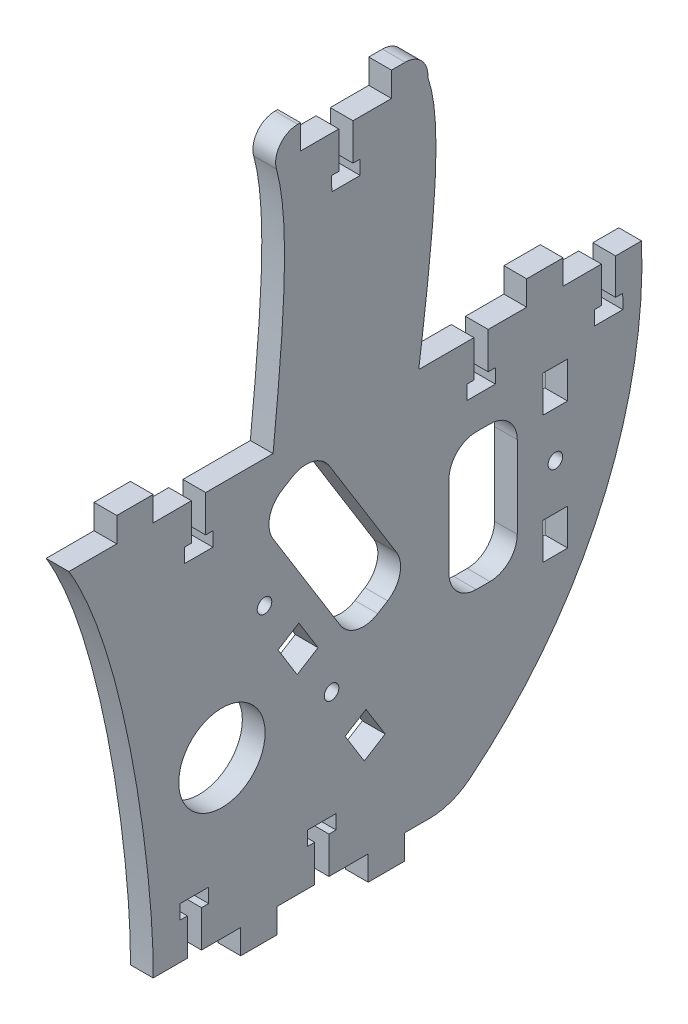
SolidWorks part; units mm, degrees
ref_plane "Front Plane" through (0, 0, 0) normal (0, 0, 1) x (1, 0, 0)
ref_plane "Top Plane" through (0, 0, 0) normal (0, 1, 0) x (1, 0, 0)
ref_plane "Right Plane" through (0, 0, 0) normal (1, 0, 0) x (0, 0, -1)
sketch "Sketch1" plane through (0, 0, 0) normal (1, 0, 0) x (0, 0, -1)
  line L0 (0, 110) -> (159.8137, 110)
  line L1 (106.68, 0) -> (0, 0)
  line L2 (0, 0) -> (0, 110)
  line L3 (36.2253, 95.776) -> (36.2253, 114.63) construction
  line L4 (74.3728, 96) -> (74.3728, 116.6546) construction
  line L5 (115.062, 95.776) -> (115.062, 119.2692) construction
  line L6 (23.5253, -5.9944) -> (23.5253, 146.3399) construction
  line L7 (35.0028, 14.224) -> (35.0028, 4.4881) construction
  line L8 (70.5628, 14.224) -> (70.5628, 4.0689) construction
  line L9 (77.3365, 179.3005) -> (77.3365, 182.7862) construction
  line L10 (61.2755, 63.6608) -> (66.6243, 55.0228) construction
  line L12 (85.3452, 24.7896) -> (40.7447, 96.8169) construction
  line L13 (56.9924, 110) -> (95.7389, 110)
  line L14 (135.7653, 91.7849) -> (135.7653, 46.0648) construction
  line L15 (0, 0) -> (4.645, 0)
  line L16 (0, 0) -> (0, 106.026)
  line L17 (64.6365, 179.3005) -> (90.0365, 179.3005)
  line L18 (77.3365, 165.0765) -> (77.3365, 176.5985) construction
  line L21 (150.622, 96) -> (150.622, 123.1211) construction
  line L22 (59.4414, 99.9132) -> (62.2149, 101.6307)
  line L23 (56.9744, 89.4231) -> (75.6953, 59.19)
  line L24 (86.1854, 56.723) -> (88.959, 58.4404)
  line L25 (72.705, 99.1637) -> (91.4259, 68.9306)
  line L27 (113.7019, 86.9157) -> (117.5119, 86.9157)
  line L28 (106.0819, 79.2957) -> (106.0819, 56.4357)
  line L29 (113.7019, 48.8157) -> (117.5119, 48.8157)
  line L30 (125.1319, 79.2957) -> (125.1319, 56.4357)
  arc A0 (159.8137, 110) -> (106.68, 0) centre (30.2941, 104.7297) cw
  circle A1 centre (73.3103, 44.2252) radius 2.032
  circle A2 centre (54.5895, 74.4584) radius 2.032
  arc A3 (72.705, 99.1637) -> (62.2149, 101.6307) centre (66.2265, 95.1521) ccw
  circle A4 centre (135.7653, 68.9249) radius 2.032
  arc A5 (56.9744, 89.4231) -> (59.4414, 99.9132) centre (63.453, 93.4347) cw
  arc A6 (86.1854, 56.723) -> (75.6953, 59.19) centre (82.1738, 63.2016) cw
  arc A7 (88.959, 58.4404) -> (91.4259, 68.9306) centre (84.9474, 64.919) ccw
  arc A8 (113.7019, 86.9157) -> (106.0819, 79.2957) centre (113.7019, 79.2957) ccw
  arc A9 (117.5119, 86.9157) -> (125.1319, 79.2957) centre (117.5119, 79.2957) cw
  arc A10 (125.1319, 56.4357) -> (117.5119, 48.8157) centre (117.5119, 56.4357) cw
  arc A11 (113.7019, 48.8157) -> (106.0819, 56.4357) centre (113.7019, 56.4357) cw
  circle A13 centre (42.7143, 43.634) radius 12.049
  spline S0 degree 3 poles (54.4765, 186.1585) (63.2335, 173.4813) (60.1129, 141.7407) (56.9924, 110) knots 0 0 0 0 1 1 1 1
  spline S1 degree 3 poles (23.5253, 0) (23.8864, 21.7728) (16.984, 81.5035) (0, 110) knots 0 0 0 0 1 1 1 1
  spline S2 degree 3 poles (94.1234, 188.6516) (104.3412, 179.5615) (104.713, 162.5405) (97.6324, 110) knots 0 0 0 0 1 1 1 1
  point P62 (95.4375, 62.4521)
  point P65 (106.0819, 86.9157)
  point P72 (106.0819, 48.8157)
  line B0 (34.2129, 110) -> (34.2129, 99.7448)
  line B1 (34.2129, 99.7448) -> (32.2286, 99.7448)
  line B2 (32.2286, 99.7448) -> (32.2566, 95.776)
  line B3 (32.2566, 95.776) -> (40.1941, 95.776)
  line B4 (40.1941, 95.776) -> (40.1661, 99.7448)
  line B5 (40.1661, 99.7448) -> (38.1817, 99.7448)
  line B6 (38.1817, 99.7448) -> (38.1817, 110)
  line B7 (18.4453, 116.858) -> (18.4453, 110) construction
  line B8 (13.3653, 116.858) -> (23.5253, 116.858)
  line B9 (13.3653, 116.858) -> (13.3653, 110)
  line B10 (13.3653, 110) -> (23.5253, 110)
  line B11 (23.5253, 116.858) -> (23.5253, 110)
  line B12 (113.0496, 110) -> (113.0496, 99.7448)
  line B13 (113.0496, 99.7448) -> (111.0652, 99.7448)
  line B14 (111.0652, 99.7448) -> (111.0932, 95.776)
  line B15 (111.0932, 95.776) -> (119.0307, 95.776)
  line B16 (119.0307, 95.776) -> (119.0027, 99.7448)
  line B17 (119.0027, 99.7448) -> (117.0183, 99.7448)
  line B18 (117.0183, 99.7448) -> (117.0183, 110)
  line B19 (1894.7464, 116.858) -> (1894.7464, 110) construction
  line B20 (1889.6664, 116.858) -> (1899.8264, 116.858)
  line B21 (1889.6664, 116.858) -> (1889.6664, 110)
  line B22 (1889.6664, 110) -> (1899.8264, 110)
  line B23 (1899.8264, 116.858) -> (1899.8264, 110)
  line B24 (132.3245, 86.7129) -> (139.1825, 86.697) construction
  line B25 (132.3127, 81.6329) -> (132.3363, 91.7929)
  line B26 (132.3127, 81.6329) -> (139.1707, 81.617)
  line B27 (139.1707, 81.617) -> (139.1943, 91.777)
  line B28 (132.3363, 91.7929) -> (139.1943, 91.777)
  line B29 (132.3245, 51.1368) -> (139.1825, 51.1527) construction
  line B30 (132.3363, 46.0568) -> (132.3127, 56.2168)
  line B31 (132.3363, 46.0568) -> (139.1943, 46.0728)
  line B32 (139.1943, 46.0728) -> (139.1707, 56.2327)
  line B33 (132.3127, 56.2168) -> (139.1707, 56.2327)
  line B34 (85.5861, 30.9138) -> (79.7554, 27.3034) construction
  line B35 (82.9117, 35.2329) -> (88.2605, 26.5948)
  line B36 (82.9117, 35.2329) -> (77.081, 31.6224)
  line B37 (77.081, 31.6224) -> (82.4298, 22.9844)
  line B38 (88.2605, 26.5948) -> (82.4298, 22.9844)
  line B39 (66.8652, 61.147) -> (61.0346, 57.5365) construction
  line B40 (64.1908, 65.466) -> (69.5397, 56.828)
  line B41 (64.1908, 65.466) -> (58.3602, 61.8556)
  line B42 (58.3602, 61.8556) -> (63.709, 53.2175)
  line B43 (69.5397, 56.828) -> (63.709, 53.2175)
  line B44 (132.842, 116.858) -> (132.842, 110) construction
  line B45 (127.762, 116.858) -> (137.922, 116.858)
  line B46 (127.762, 116.858) -> (127.762, 110)
  line B47 (127.762, 110) -> (137.922, 110)
  line B48 (137.922, 116.858) -> (137.922, 110)
  line B49 (168.402, 116.858) -> (168.402, 110) construction
  line B50 (163.322, 116.858) -> (173.482, 116.858)
  line B51 (163.322, 116.858) -> (163.322, 110)
  line B52 (163.322, 110) -> (173.482, 110)
  line B53 (173.482, 116.858) -> (173.482, 110)
  line B54 (148.6096, 110.224) -> (148.6096, 99.9687)
  line B55 (148.6096, 99.9687) -> (146.6252, 99.9687)
  line B56 (146.6252, 99.9687) -> (146.6532, 96)
  line B57 (146.6532, 96) -> (154.5907, 96)
  line B58 (154.5907, 96) -> (154.5627, 99.9687)
  line B59 (154.5627, 99.9687) -> (152.5783, 99.9687)
  line B60 (152.5783, 99.9687) -> (152.5783, 110.224)
  line B61 (59.5565, 186.1585) -> (59.5565, 179.3005) construction
  line B62 (54.4765, 186.1585) -> (64.6365, 186.1585)
  line B63 (54.4765, 186.1585) -> (54.4765, 179.3005)
  line B64 (54.4765, 179.3005) -> (64.6365, 179.3005)
  line B65 (64.6365, 186.1585) -> (64.6365, 179.3005)
  line B66 (95.1165, 186.1585) -> (95.1165, 179.3005) construction
  line B67 (90.0365, 186.1585) -> (100.1965, 186.1585)
  line B68 (90.0365, 186.1585) -> (90.0365, 179.3005)
  line B69 (90.0365, 179.3005) -> (100.1965, 179.3005)
  line B70 (100.1965, 186.1585) -> (100.1965, 179.3005)
  line B71 (37.0152, 0) -> (37.0152, 10.2552)
  line B72 (37.0152, 10.2552) -> (38.9996, 10.2552)
  line B73 (38.9996, 10.2552) -> (38.9716, 14.224)
  line B74 (38.9716, 14.224) -> (31.0341, 14.224)
  line B75 (31.0341, 14.224) -> (31.0621, 10.2553)
  line B76 (31.0621, 10.2553) -> (33.0465, 10.2553)
  line B77 (33.0465, 10.2553) -> (33.0465, 0)
  line B78 (72.5752, 0) -> (72.5752, 10.2552)
  line B79 (72.5752, 10.2552) -> (74.5596, 10.2552)
  line B80 (74.5596, 10.2552) -> (74.5316, 14.224)
  line B81 (74.5316, 14.224) -> (66.5941, 14.224)
  line B82 (66.5941, 14.224) -> (66.6221, 10.2552)
  line B83 (66.6221, 10.2552) -> (68.6065, 10.2552)
  line B84 (68.6065, 10.2552) -> (68.6065, 0)
  line B85 (88.5968, 0) -> (88.5968, -6.858) construction
  line B86 (83.5168, 0) -> (93.6768, 0)
  line B87 (83.5168, 0) -> (83.5168, -6.858)
  line B88 (83.5168, -6.858) -> (93.6768, -6.858)
  line B89 (93.6768, 0) -> (93.6768, -6.858)
  line B90 (53.0368, 0) -> (53.0368, -6.858) construction
  line B91 (47.9568, 0) -> (58.1168, 0)
  line B92 (47.9568, 0) -> (47.9568, -6.858)
  line B93 (47.9568, -6.858) -> (58.1168, -6.858)
  line B94 (58.1168, 0) -> (58.1168, -6.858)
  line B95 (75.324, 179.3005) -> (75.324, 169.0452)
  line B96 (75.324, 169.0452) -> (73.3397, 169.0452)
  line B97 (73.3397, 169.0452) -> (73.3677, 165.0765)
  line B98 (73.3677, 165.0765) -> (81.3052, 165.0765)
  line B99 (81.3052, 165.0765) -> (81.2772, 169.0452)
  line B100 (81.2772, 169.0452) -> (79.2928, 169.0452)
  line B101 (79.2928, 169.0452) -> (79.2928, 179.3005)
  dimension "D15" = 17.78
  dimension "D14" = 17.78
  dimension "D33" = 4.064
  dimension "D34" = 4.064
  dimension "D35" = 4.064
  dimension "D2" = 110
  dimension "D3" = 106.68
  dimension "D5" = 17.78
  dimension "D6" = 17.78
  dimension "D7" = 160.1167
  dimension "D8" = 17.78
  dimension "D9" = 17.78
  dimension "D10" = 76.2
  dimension "D11" = 17.78
  dimension "D12" = 17.78
  dimension "D13" = 17.78
  dimension "D26" = 25.4
  dimension "D31" = 40.64
sketch_block_instance "Block1-1"
sketch_block "Block1" parameters "D1"=4.2151, "D2"=10.103, "D3"=7.4845, "D4"=1.829, "D5"=10.2553
sketch_block_instance "Block2-3"
sketch_block "Block2" parameters "D1"=6.858, "D2"=10.16
sketch_block_instance "Block1-8"
sketch_block_instance "Block2-6"
sketch_block_instance "Block2-11"
sketch_block_instance "Block2-12"
sketch_block_instance "Block2-14"
sketch_block_instance "Block2-15"
sketch_block_instance "Block2-16"
sketch_block_instance "Block2-17"
sketch_block_instance "Block1-15"
sketch_block_instance "Block2-21"
sketch_block_instance "Block2-22"
sketch_block_instance "Block1-19"
sketch_block_instance "Block1-20"
sketch_block_instance "Block2-25"
sketch_block_instance "Block2-26"
sketch_block_instance "Block1-21"
extrude "Extrude1" add sketch "Sketch1" along normal blind 6.35
fillet "Fillet3" radius 17.78 1 edges at (3.175, 0, -106.68)
fillet "Fillet8" radius 6.1976 3 edges at (3.175, 186.1585, -54.4765)
fillet "Fillet10" radius 6.35 1 edges at (3.175, 186.1585, -100.1965)
